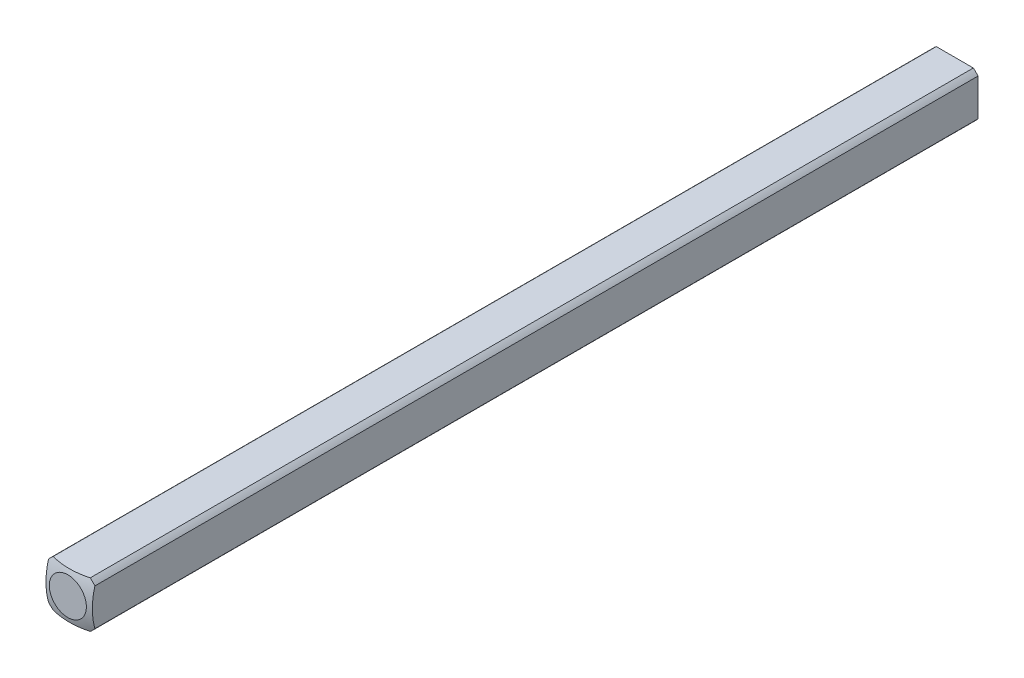
SolidWorks part; units mm, degrees
material "Custom Plastic"
ref_plane "Front Plane" through (0, 0, 0) normal (0, 0, 1) x (1, 0, 0)
ref_plane "Top Plane" through (0, 0, 0) normal (0, 1, 0) x (1, 0, 0)
ref_plane "Right Plane" through (0, 0, 0) normal (1, 0, 0) x (0, 0, -1)
sketch "Sketch1" plane through (0, 0, 0) normal (0, 0, 1) x (1, 0, 0)
  line L0 (-1.5875, -1.5875) -> (1.5875, 1.5875) construction
  line L1 (-1.5875, -1.5875) -> (1.5875, -1.5875)
  line L2 (-1.5875, -1.5875) -> (-1.5875, 1.5875)
  line L3 (-1.5875, 1.5875) -> (1.5875, 1.5875)
  line L4 (1.5875, -1.5875) -> (1.5875, 1.5875)
  dimension "D1" = 3.175
extrude "Boss-Extrude1" add sketch "Sketch1" along normal blind 152.4
sketch "Sketch2" plane through (0, 0, 0) normal (0, 0, -1) x (-1, 0, 0)
  circle A0 centre (0, 0) radius 2.032
  dimension "D1" = 4.064
extrude "Cut-Extrude1" cut sketch "Sketch2" against normal through all flip side to cut
ref_axis "Axis1" through (0, 0, 152.4) along (0, 0, -1)
sketch "Sketch3" plane through (0, 0, 0) normal (0, 1, 0) x (1, 0, 0)
  line L1 (-5.0537, -4.4027) -> (-5.0537, 5.7405)
  line L2 (-5.0537, 5.7405) -> (0, 5.7405)
  line L5 (0, -152.4) -> (0, 0) construction
  line L8 (0, 0.1609) -> (0, 5.7405)
  arc A0 (-5.0537, -4.4027) -> (0, 0.1609) centre (0, -4.9191) cw
  dimension "D1" = 5.08
revolve "Cut-Revolve1" cut sketch "Sketch3" angle 360 about axis through (0, 0, 152.4) along (0, 0, -1)
mirror "Mirror1" about plane through (0, 0, 152.4) normal (0, 0, -1) of bodies 103
sketch "Sketch4" plane through (1.5875, 0, 0) normal (1, 0, 0) x (0, 0, -1)
  line L1 (-0.2632, -1.5875) -> (-203.4632, -1.5875)
  line L2 (-0.2632, 1.5875) -> (-203.4632, 1.5875)
  line L3 (-203.4632, -1.5875) -> (-203.4632, 1.5875)
  line L4 (-0.2632, -1.5875) -> (0.8357, -1.5875)
  line L5 (0.8357, -1.5875) -> (0.8357, 1.5875)
  line L6 (0.8357, 1.5875) -> (-0.2632, 1.5875)
  dimension "D1" = 203.2
extrude "Cut-Extrude2" cut sketch "Sketch4" against normal through all
sketch "Sketch6" plane through (0, -1.5875, 0) normal (0, -1, 0) x (1, 0, 0)
  line L0 (1.5875, 203.4632) -> (1.5875, 216.1632)
  line L1 (1.5875, 203.4632) -> (1.5875, 304.5368) construction
  line L2 (1.5875, 216.1632) -> (-1.5875, 216.1632)
  line L3 (-1.5875, 304.5368) -> (-1.5875, 203.4632) construction
  line L4 (-1.5875, 216.1632) -> (-1.5875, 203.4632)
  line L5 (-1.5875, 203.4632) -> (1.5875, 203.4632)
  dimension "D1" = 12.7
extrude "Cut-Extrude3" cut sketch "Sketch6" against normal through all
sketch "Sketch7" plane through (0, -1.5875, 0) normal (0, -1, 0) x (1, 0, 0)
  line L0 (1.5875, 216.1632) -> (-1.5875, 216.1632)
  line L1 (1.5875, 216.1632) -> (1.5875, 244.1032)
  line L2 (-1.5875, 216.1632) -> (-1.5875, 244.1032)
  line L3 (1.5875, 244.1032) -> (-1.5875, 244.1032)
  dimension "D1" = 27.94
extrude "Cut-Extrude4" cut sketch "Sketch7" against normal through all
